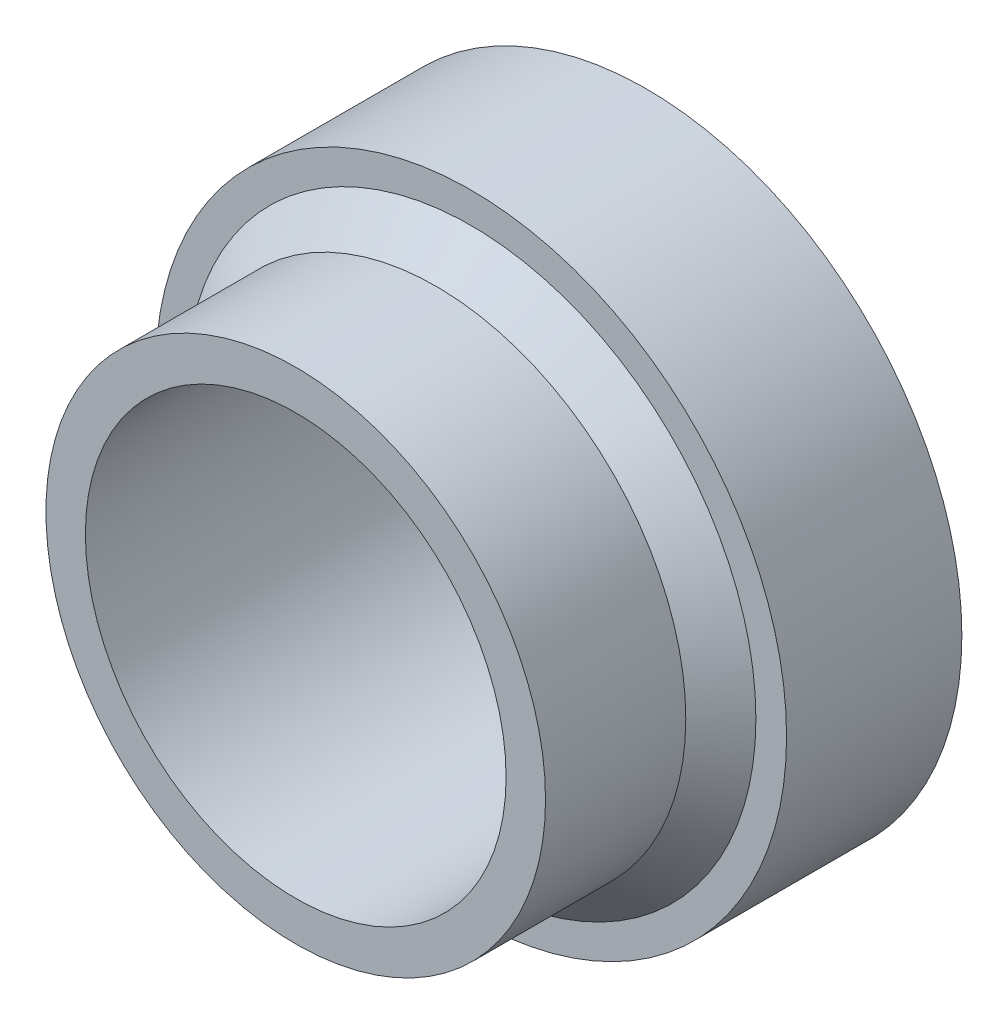
SolidWorks part; units mm, degrees
ref_plane "Front Plane" through (0, 0, 0) normal (0, 0, 1) x (1, 0, 0)
ref_plane "Top Plane" through (0, 0, 0) normal (0, 1, 0) x (1, 0, 0)
ref_plane "Right Plane" through (0, 0, 0) normal (1, 0, 0) x (0, 0, -1)
sketch "Sketch1" plane through (0, 0, 0) normal (0, 0, 1) x (1, 0, 0)
  circle A0 centre (0, 0) radius 18
  circle A1 centre (0, 0) radius 12
  dimension "D1" = 36
  dimension "D2" = 24
extrude "Boss-Extrude1" add sketch "Sketch1" along normal blind 10
sketch "Sketch3" plane through (0, 0, 0) normal (0, 0, 1) x (1, 0, 0)
  circle A0 centre (0, 0) radius 14.2
  dimension "D1" = 28.4
extrude "Cut-Extrude1" cut sketch "Sketch3" along normal blind 1.75
ref_plane "Plane2" through (0, 0, 10) normal (0, 0, 1) x (1, 0, 0)
sketch "Sketch5" plane through (0, 0, 10) normal (0, 0, 1) x (1, 0, 0)
  circle A0 centre (0, 0) radius 14.25
  circle A1 centre (0, 0) radius 12
  dimension "D1" = 28.5
extrude "Boss-Extrude2" add sketch "Sketch5" along normal blind 10
chamfer "Chamfer1" distance 2 angle 45 1 edges at (14.25, 0, 10)
